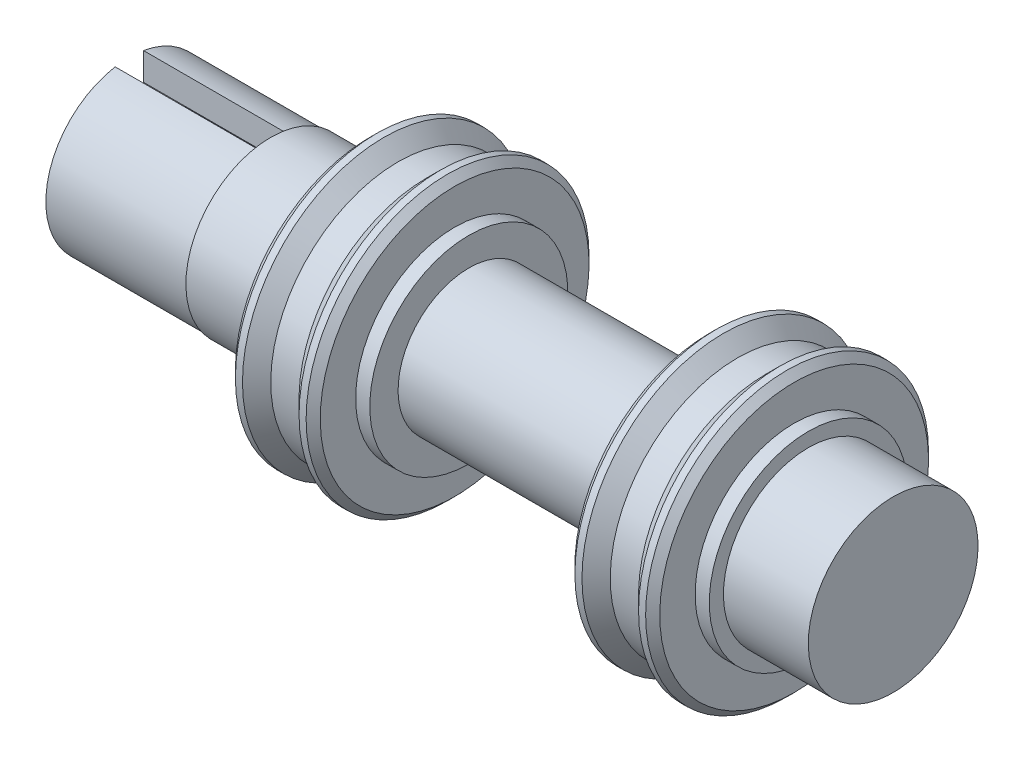
SolidWorks part; units mm, degrees
material "1.4003 (X2CrNi12)"
ref_plane "Ebene vorne" through (0, 0, 0) normal (0, 0, 1) x (1, 0, 0)
ref_plane "Ebene oben" through (0, 0, 0) normal (0, 1, 0) x (1, 0, 0)
ref_plane "Ebene rechts" through (0, 0, 0) normal (1, 0, 0) x (0, 0, -1)
sketch "Skizze1" plane through (0, 0, 0) normal (0, 0, 1) x (1, 0, 0)
  line L0 (-6, 0) -> (-6, 4) construction
  line L1 (-8, 3) -> (-11, 3)
  line L2 (-8, 3) -> (-8, 3.5)
  line L3 (-8, 3.5) -> (-7.5, 3.5)
  line L4 (-7.5, 3.5) -> (-7.5, 5)
  line L5 (-7.5, 5) -> (-7, 5)
  line L6 (-7, 5) -> (-6.5, 4.5)
  line L7 (-5.5188, 0) -> (-49.9899, 0) construction
  line L8 (-11, 3) -> (-11, 0)
  line L9 (-11, 0) -> (0, 0)
  line L10 (0, 2.5) -> (0, 0)
  line L11 (-5, 5) -> (-5.5, 4.5)
  line L12 (-4.5, 5) -> (-5, 5)
  line L13 (-4.5, 3.5) -> (-4.5, 5)
  line L14 (-4, 3.5) -> (-4.5, 3.5)
  line L15 (-4, 2.5) -> (-4, 3.5)
  line L16 (-4, 2.5) -> (0, 2.5)
  line L19 (-6.5, 4.5) -> (-5.5, 4.5)
  line L20 (-6.5, 4.5) -> (-6, 4) construction
  line L21 (-6, 4) -> (-5.5, 4.5) construction
  dimension "D1" = 6
  dimension "D2" = 0.5
  dimension "D3" = 10
  dimension "D4" = 9
  dimension "D5" = 4
  dimension "D6" = 0.5
  dimension "D7" = 3
  dimension "D8" = 4
  dimension "D9" = 5
  dimension "D11" = 2
revolve "Rotation1" add sketch "Skizze1" angle 360 about L7
chamfer "Fase1" distance 0.25 angle 45 2 edges at (-4.5, 5, 0) (-7.5, 5, 0)
mirror "Spiegeln1" about plane through (0, 0, 0) normal (1, 0, 0) of bodies 101
ref_plane "Ebene1" through (-6, 0, 0) normal (-1, 0, 0) x (0, 0, 1)
ref_plane "Ebene2" through (6, 0, 0) normal (-1, 0, 0) x (0, 0, 1)
sketch "Skizze2" plane through (-11, 0, 0) normal (-1, 0, 0) x (0, 0, 1)
  line L0 (-0.5, -1.9365) -> (-0.5, -2.9073)
  line L1 (0.5, -1.9365) -> (0.5, -2.9073)
  line L2 (-0.5, 2.9073) -> (-0.5, 1.9365)
  line L3 (0, 3) -> (0, -3) construction
  line L4 (0.5, 2.9073) -> (0.5, 1.9365)
  arc A0 (-0.5, 1.9365) -> (-0.5, -1.9365) centre (0, 0) ccw
  circle A1 centre (0, 0) radius 3 construction
  arc A2 (-0.5, 2.9073) -> (-0.5, -2.9073) centre (0, 0) ccw
  arc A3 (0.5, -1.9365) -> (0.5, 1.9365) centre (0, 0) ccw
  arc A4 (0.5, -2.9073) -> (0.5, 2.9073) centre (0, 0) ccw
  circle A5 centre (0, 0) radius 3 construction
  dimension "D1" = 4
  dimension "D3" = 2.95
  dimension "D2" = 1
extrude "Aufsatz-Linear austragen1" add sketch "Skizze2" along normal blind 5
